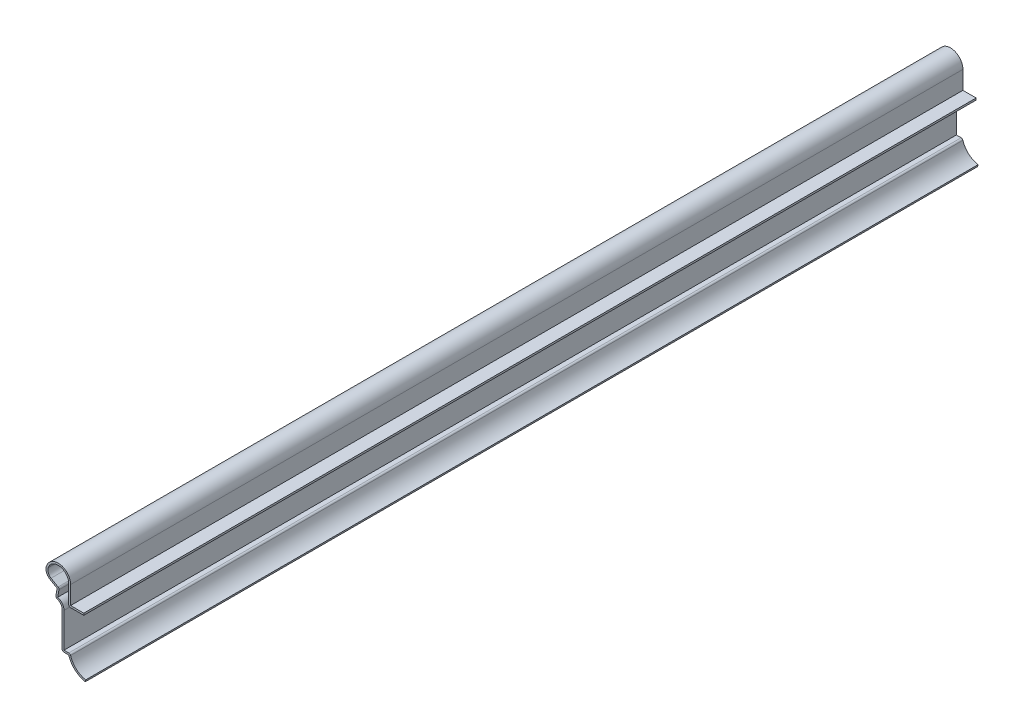
SolidWorks part; units mm, degrees
ref_plane "Front Plane" through (0, 0, 0) normal (0, 0, 1) x (1, 0, 0)
ref_plane "Top Plane" through (0, 0, 0) normal (0, 1, 0) x (1, 0, 0)
ref_plane "Right Plane" through (0, 0, 0) normal (1, 0, 0) x (0, 0, -1)
sketch "Sketch3" plane through (0, 0, 0) normal (0, 0, 1) x (1, 0, 0)
  line L0 (24.781, 42.7805) -> (24.781, -0.082) construction
  dimension "D1" = 42.8625
sketch "Sketch1" plane through (0, 0, 0) normal (0, 0, 1) x (1, 0, 0)
  line L0 (7.9375, 7.1437) -> (11.1125, 7.1437)
  line L1 (11.1125, 7.1437) -> (11.1125, 24.6062)
  line L2 (14.2875, 27.7812) -> (13.5177, 32.1469)
  line L3 (13.5177, 32.1469) -> (16.8986, 34.0989)
  line L4 (7.0783, 36.9094) -> (7.0783, 28.1781)
  line L5 (7.0783, 28.1781) -> (0.7283, 28.1781)
  arc A0 (0, 0) -> (7.9375, 7.1437) centre (-1.9381, 10.1351) ccw
  arc A1 (11.1125, 24.6062) -> (14.2875, 27.7812) centre (14.2875, 24.6062) cw
  arc A2 (16.8986, 34.0989) -> (18.68, 38.7889) centre (14.9143, 37.5359) ccw
  arc A3 (18.68, 38.7889) -> (7.0783, 36.9094) centre (13.0314, 36.9094) ccw
  arc A4 (-0.167, 0.8732) -> (7.0867, 7.4015) centre (-1.9381, 10.1351) ccw construction
  point P15 (0, 0)
  point P17 (17.5487, 40.5257)
  point P20 (11.4067, 7.3574)
  point P21 (11.1645, 24.6559)
  point P22 (15.0702, 27.4782)
  point P23 (15.161, 27.5085)
  point P24 (0, 0)
  point P25 (0, 0)
  point P26 (6.0837, 28.4494)
  point P27 (9.1204, 6.9791)
  point P28 (17.7112, 33.7511)
  point P29 (15.2603, 27.6285)
  point P30 (14.5892, 32.3314)
  point P31 (14.9448, 27.7126)
  point P32 (16.4108, 33.1974)
  point P33 (15.0392, 27.691)
  point P34 (0, 0)
  point P35 (13.5177, 32.1469)
  point P36 (17.3526, 41.3928)
  point P37 (6.9263, 28.1595)
  point P38 (16.928, 34.1158)
  point P39 (0.6705, 28.0793)
  dimension "D1" = 42.8625
  dimension "D2" = 0.889
  dimension "D7" = 3.175
  dimension "D8" = 10
  dimension "D13" = 3.9688
  dimension "D14" = 5.9531
  dimension "D4" = 10.3187
  dimension "D3" = 19.05
  dimension "D5" = 3.175
  dimension "D6" = 17.4625
  dimension "D9" = 4.3656
  dimension "D10" = 11.1125
  dimension "D11" = 7.1437
  dimension "D12" = 30
  dimension "D15" = 6.35
  dimension "D16" = 28.1781
extrude "Extrude-Thin1" add sketch "Sketch1" against normal blind 428.625 thin contours A0 L0 L1 A1 L2 L3 A2 A3 L4 L5 thin type one direction reverse wall 0.889
fillet "Fillet1" radius 0.889 5 edges at (7.2543, 8.0328, -214.3125) (11.1125, 7.1437, -214.3125) (12.5341, 32.6055, -214.3125) (14.2875, 27.7812, -214.3125) (7.9673, 27.2891, -214.3125)
mirror "Mirror1" about plane through (0.7283, 27.2891, -428.625) normal (1, 0, 0) of bodies 102
delete or keep bodies "Body-Delete/Keep 1" type delete bodies bodies 102
